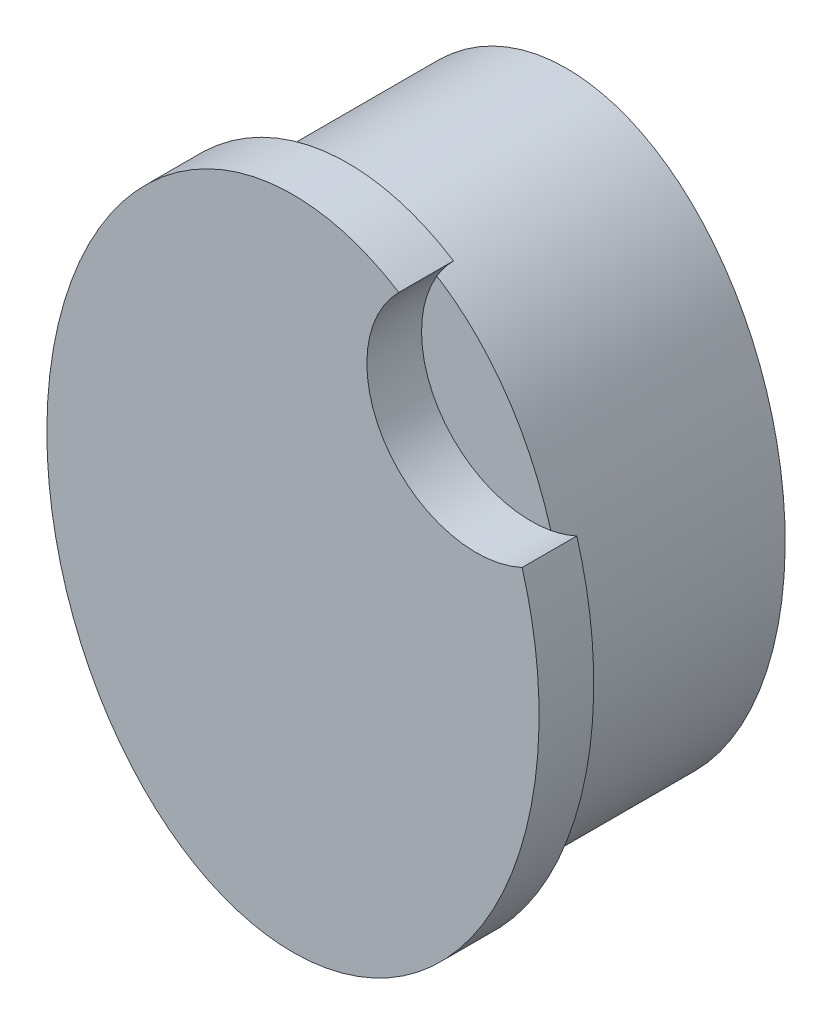
SolidWorks part; units mm, degrees
ref_plane "Alzado" through (0, 0, 0) normal (0, 0, 1) x (1, 0, 0)
ref_plane "Planta" through (0, 0, 0) normal (0, 1, 0) x (1, 0, 0)
ref_plane "Vista lateral" through (0, 0, 0) normal (1, 0, 0) x (0, 0, -1)
sketch "Croquis1" plane through (0, 0, 0) normal (0, 0, 1) x (1, 0, 0)
  ellipse E0 centre (0, 0) end of major axis (0, 11) minor radius 8
extrude "Saliente-Extruir1" add sketch "Croquis1" along normal blind 8
sketch "Croquis2" plane through (0, 0, 8) normal (0, 0, 1) x (1, 0, 0)
  ellipse E0 centre (0, 0) end of major axis (0, 12) minor radius 9
extrude "Saliente-Extruir2" add sketch "Croquis2" along normal blind 2
sketch "Croquis3" plane through (0, 0, 10) normal (0, 0, 1) x (1, 0, 0)
  line L0 (0, 0) -> (0, 3.9368)
  line L1 (0, 3.9368) -> (-4, 3.9368)
  line L2 (0, 3.9368) -> (4, 3.9368)
  circle A0 centre (6.7024, 8.0087) radius 4
  ellipse E0 centre (-4, 3.9368) end of major axis (-6.2516, 7.2429) minor radius 2
  ellipse E1 centre (4, 3.9368) end of major axis (6.2681, 7.2316) minor radius 2
  ellipse E2 centre (0, 0) end of major axis (0, 12) minor radius 9 construction
  ellipse M3 centre (0, 0) end of major axis (0, 12) minor radius 9
extrude "Cortar-Extruir1" cut sketch "Croquis3" against normal blind 2 contours A0 E1 | E1 A0 M3
